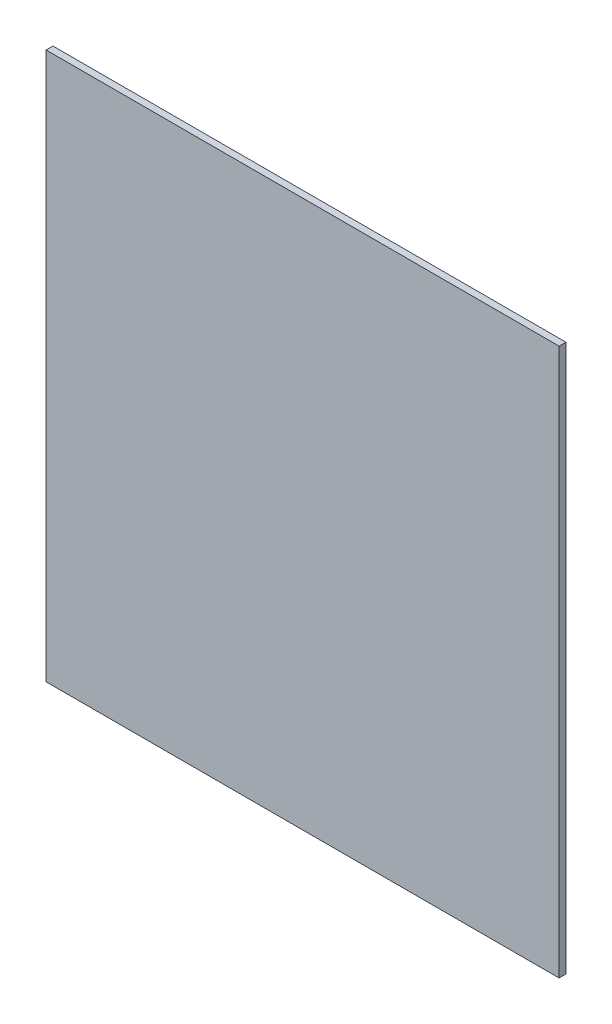
SolidWorks part; units mm, degrees
ref_plane "Front Plane" through (0, 0, 0) normal (0, 0, 1) x (1, 0, 0)
ref_plane "Top Plane" through (0, 0, 0) normal (0, 1, 0) x (1, 0, 0)
ref_plane "Right Plane" through (0, 0, 0) normal (1, 0, 0) x (0, 0, -1)
sketch "Sketch1" plane through (0, 0, 0) normal (0, 0, 1) x (1, 0, 0)
  line L8 (163, 232.1) -> (13, 232.1)
  line L9 (163, 72.1) -> (163, 232.1)
  line L10 (13, 72.1) -> (163, 72.1)
  line L11 (13, 232.1) -> (13, 72.1)
  point P2 (0, 0)
  dimension "D1" = 150
  dimension "D2" = 160
extrude "Side_doors" add sketch "Sketch1" against normal blind 2
